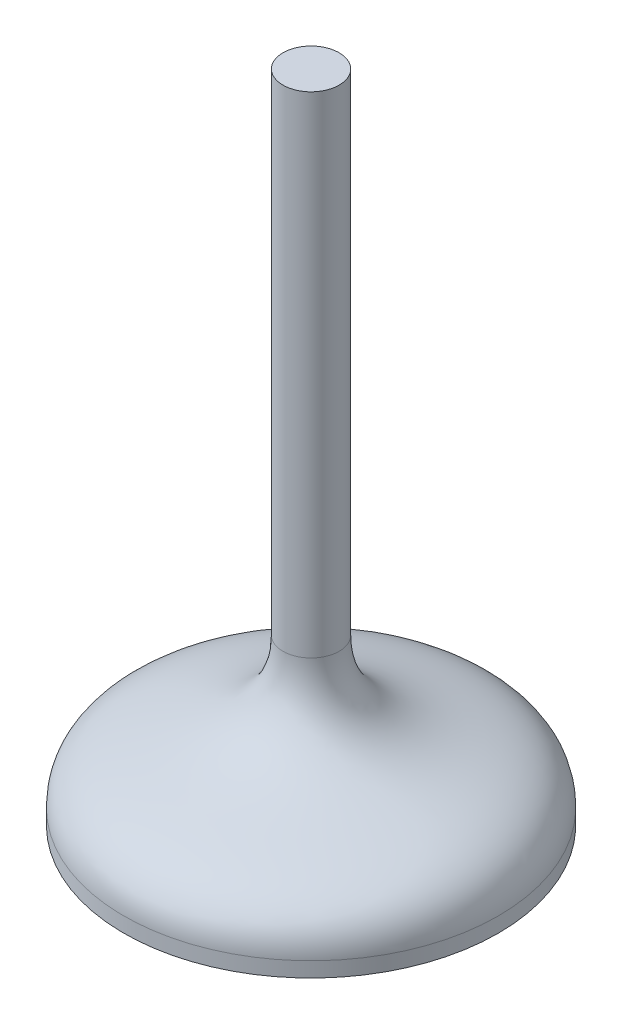
SolidWorks part; units mm, degrees
ref_plane "Front" through (0, 0, 0) normal (0, 0, 1) x (1, 0, 0)
ref_plane "Top" through (0, 0, 0) normal (0, 1, 0) x (1, 0, 0)
ref_plane "Right" through (0, 0, 0) normal (1, 0, 0) x (0, 0, -1)
sketch "Sketch1" plane through (0, 0, 0) normal (0, 0, 1) x (1, 0, 0)
  line L0 (-10, 0) -> (10, 0)
  line L1 (0, 0) -> (0, 35)
  line L2 (-10, 0) -> (-10, 0.8)
  line L3 (0, 35) -> (-1.5, 35)
  line L4 (-1.5, 35) -> (-1.5, 8.8)
  spline S0 degree 3 poles (-10, 0.8) (-10, 5.1438) (-1.5, 2.7062) (-1.5, 8.8) knots 0 0 0 0 1 1 1 1
  point P8 (0, 0)
  point P9 (-1.5, 9.6985)
  dimension "D1" = 20
  dimension "D2" = 35
  dimension "D3" = 0.8
  dimension "D4" = 1.5
  dimension "D5" = 8
revolve "Revolve1" add sketch "Sketch1" angle 360 about L1
